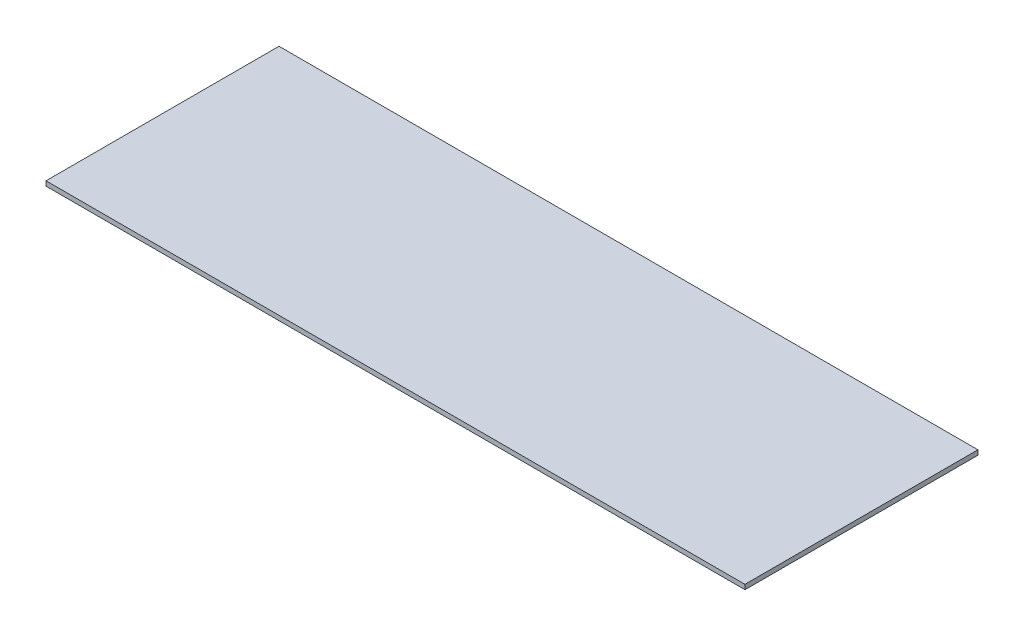
SolidWorks part; units mm, degrees
ref_plane "Front Plane" through (0, 0, 0) normal (0, 0, 1) x (1, 0, 0)
ref_plane "Top Plane" through (0, 0, 0) normal (0, 1, 0) x (1, 0, 0)
ref_plane "Right Plane" through (0, 0, 0) normal (1, 0, 0) x (0, 0, -1)
sketch "Sketch1" plane through (0, 0, 0) normal (0, 1, 0) x (1, 0, 0)
  line L1 (-150, -50) -> (150, -50)
  line L2 (-150, -50) -> (-150, 50)
  line L3 (-150, 50) -> (150, 50)
  line L4 (150, -50) -> (150, 50)
  line L5 (-150, -50) -> (150, 50) construction
  line L6 (-150, 50) -> (150, -50) construction
  point P0 (0, 0)
  dimension "D1" = 100
  dimension "D2" = 300
extrude "Boss-Extrude1" add sketch "Sketch1" along normal blind 2
sketch "Sketch2" plane through (0, 0, 50) normal (0, 0, 1) x (1, 0, 0)
  line L0 (-150, 2) -> (-149.9651, 0)
  line L1 (-150, 0) -> (150, 0) construction
  line L2 (-149.9651, 0) -> (-150, 0)
  line L3 (-150, 0) -> (-150, 2)
  line L4 (150, 0) -> (149.9651, 2)
  line L5 (-150, 2) -> (150, 2) construction
  line L6 (149.9651, 2) -> (150, 2)
  line L7 (150, 2) -> (150, 0)
  dimension "D1" = 1
  dimension "D2" = 1
extrude "Cut-Extrude1" cut sketch "Sketch2" against normal through all
